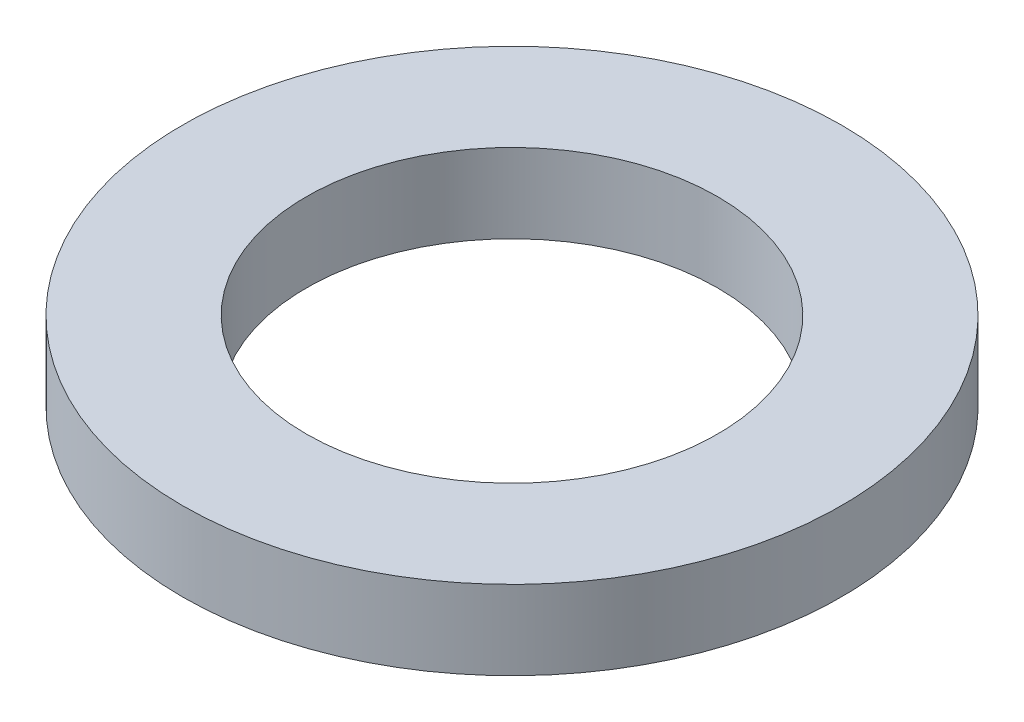
SolidWorks part; units mm, degrees
ref_plane "Front Plane" through (0, 0, 0) normal (0, 0, 1) x (1, 0, 0)
ref_plane "Top Plane" through (0, 0, 0) normal (0, 1, 0) x (1, 0, 0)
ref_plane "Right Plane" through (0, 0, 0) normal (1, 0, 0) x (0, 0, -1)
sketch "Sketch1" plane through (0, 0, 0) normal (0, 1, 0) x (1, 0, 0)
  circle A0 centre (0, 0) radius 7.9375
  dimension "OD" = 15.875
extrude "Boss-Extrude1" add sketch "Sketch1" along normal blind 1.905
sketch "Sketch5" plane through (0, 1.905, 0) normal (0, 1, 0) x (-1, 0, 0)
  circle A0 centre (0, 0) radius 4.953
  dimension "ID" = 9.906
extrude "Cut-Extrude1" cut sketch "Sketch5" against normal through all
